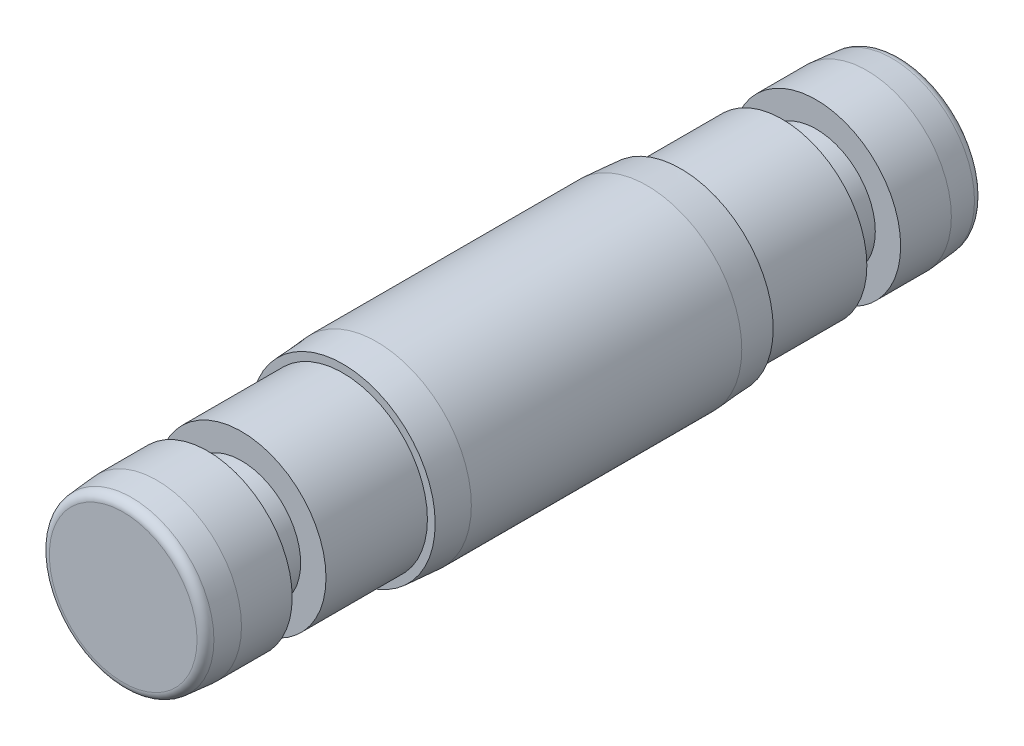
SolidWorks part; units mm, degrees
material "Chrome Stainless Steel"
ref_plane "Front Plane" through (0, 0, 0) normal (0, 0, 1) x (1, 0, 0)
ref_plane "Top Plane" through (0, 0, 0) normal (0, 1, 0) x (1, 0, 0)
ref_plane "Right Plane" through (0, 0, 0) normal (1, 0, 0) x (0, 0, -1)
sketch "Sketch1" plane through (0, 0, 0) normal (1, 0, 0) x (0, 0, -1)
  line L0 (-10, 0) -> (-3, 0)
  line L2 (-10, 4.3688) -> (-10, 0)
  line L3 (-3, 3.5) -> (-5, 3.5)
  line L4 (-8, 5) -> (-9.5, 4.8688)
  line L5 (-5, 3.5) -> (-5, 5)
  line L6 (-5, 5) -> (-8, 5)
  line L7 (-3, 3.5) -> (-3, 5)
  line L8 (-3, 5) -> (3, 5)
  line L9 (-3, 0) -> (13, 0)
  line L10 (3, 5) -> (3, 5.4601)
  line L11 (3, 5.4601) -> (5, 5.6)
  line L12 (5, 5.6) -> (13, 5.6)
  line L13 (13, 5.6) -> (13, 0)
  arc A0 (-9.5, 4.8688) -> (-10, 4.3688) centre (-9.5, 4.3688) ccw
  point P4 (0, 0)
  dimension "D4" = 2
  dimension "D5" = 0.5
  dimension "D1" = 3.5
  dimension "D2" = 2
  dimension "D3" = 13
  dimension "D6" = 4
  dimension "D7" = 2
  dimension "D8" = 8
  dimension "D9" = 5.6
  dimension "D10" = 5
  dimension "D11" = 5
  dimension "D12" = 7
  dimension "D13" = 1.5
  dimension "D14" = 1.5
  dimension "D15" = 4.3688
  dimension "D16" = 1.5057
revolve "Revolve1" add sketch "Sketch1" angle 360 about L9
ref_plane "Plane1" through (0, 0, -13) normal (0, 0, -1) x (-1, 0, 0)
mirror "Mirror1" about plane through (0, 0, -13) normal (0, 0, -1) of "Revolve1"
